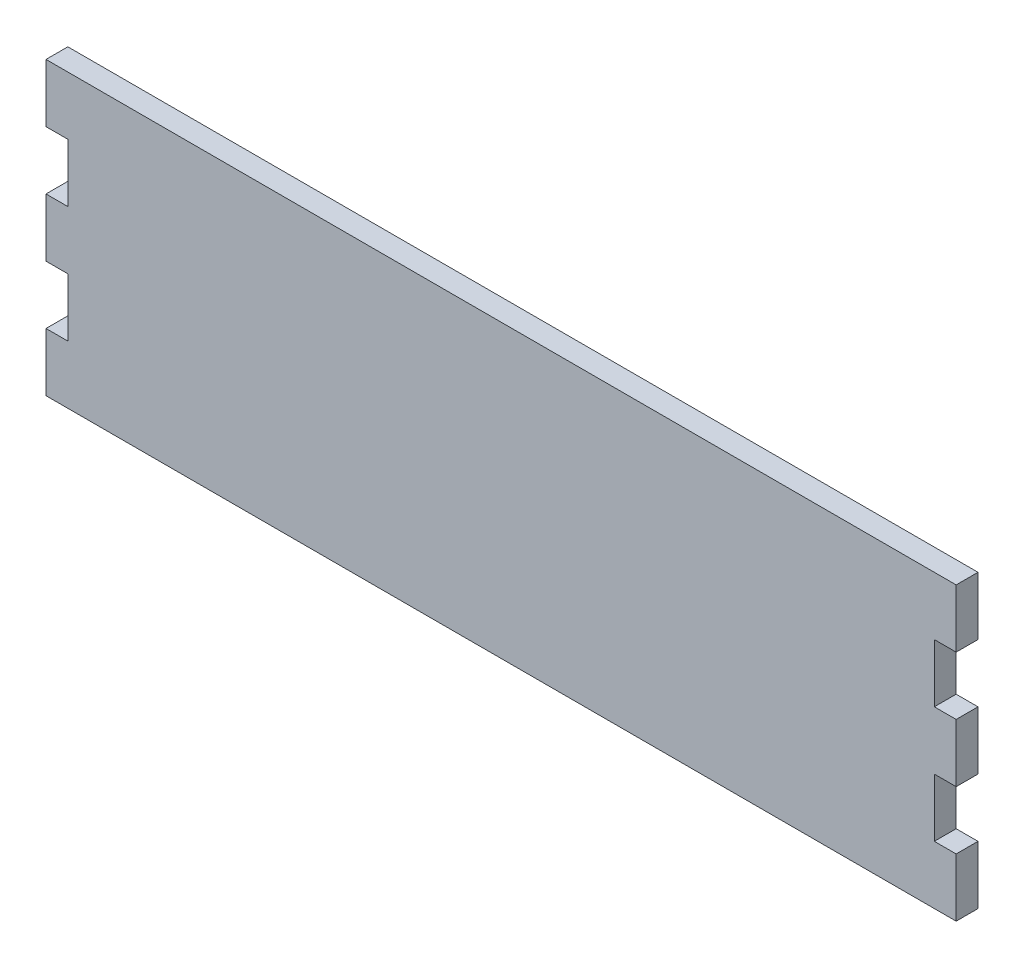
SolidWorks part; units mm, degrees
ref_plane "Alzado" through (0, 0, 0) normal (0, 0, 1) x (1, 0, 0)
ref_plane "Planta" through (0, 0, 0) normal (0, 1, 0) x (1, 0, 0)
ref_plane "Vista lateral" through (0, 0, 0) normal (1, 0, 0) x (0, 0, -1)
sketch "Croquis1" plane through (0, 0, 0) normal (0, 0, 1) x (1, 0, 0)
  line L1 (125, -40) -> (-125, -40)
  line L2 (125, -40) -> (125, 40)
  line L3 (125, 40) -> (-125, 40)
  line L4 (-125, -40) -> (-125, 40)
  line L5 (125, -40) -> (-125, 40) construction
  line L6 (125, 40) -> (-125, -40) construction
  point P0 (0, 0)
  dimension "D1" = 250
  dimension "D2" = 80
extrude "Saliente-Extruir1" add sketch "Croquis1" along normal blind 6
sketch "Croquis2" plane through (0, 0, 6) normal (0, 0, 1) x (1, 0, 0)
  line L0 (0, 40) -> (0, -40) construction
  line L1 (125, 40) -> (-125, 40) construction
  line L2 (-125, -40) -> (125, -40) construction
  line L3 (0, 0) -> (-125, 0) construction
  line L4 (-125, 40) -> (-125, -40) construction
  line L5 (0, 24) -> (-125, 24) construction
  line L6 (-125, -8) -> (-119, -8)
  line L7 (-125, 24) -> (-119, 24)
  line L8 (-125, 24) -> (-125, 8)
  line L9 (-125, 8) -> (-119, 8)
  line L10 (-119, 24) -> (-119, 8)
  line L11 (-119, -24) -> (-119, -8)
  line L12 (-125, -24) -> (-119, -24)
  line L13 (-125, -24) -> (-125, -8)
  line L14 (125, -24) -> (125, -8)
  line L15 (125, -24) -> (119, -24)
  line L16 (119, -24) -> (119, -8)
  line L17 (125, -8) -> (119, -8)
  line L18 (125, 8) -> (119, 8)
  line L19 (119, 24) -> (119, 8)
  line L20 (125, 24) -> (119, 24)
  line L21 (125, 24) -> (125, 8)
  dimension "D1" = 16
  dimension "D2" = 6
  dimension "D3" = 8
extrude "Cortar-Extruir1" cut sketch "Croquis2" against normal blind 6
